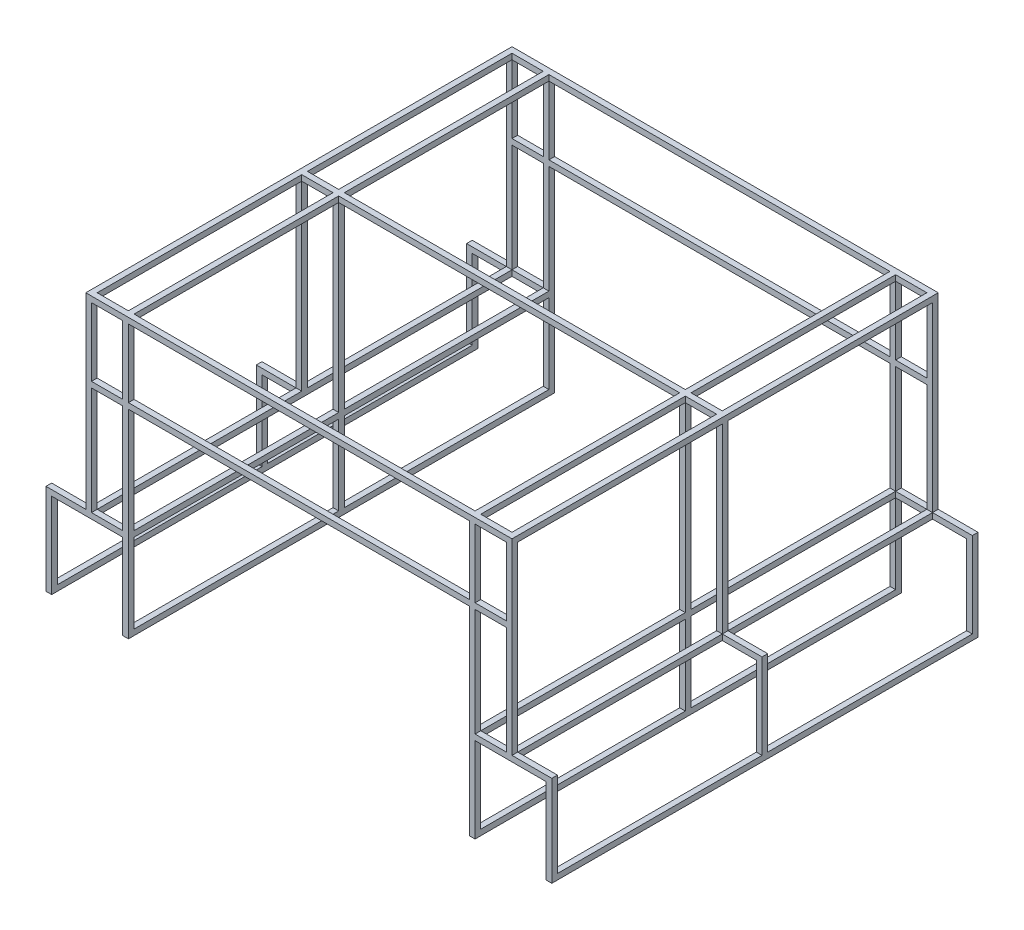
SolidWorks part; units mm, degrees
ref_plane "Front Plane" through (0, 0, 0) normal (0, 0, 1) x (1, 0, 0)
ref_plane "Top Plane" through (0, 0, 0) normal (0, 1, 0) x (1, 0, 0)
ref_plane "Right Plane" through (0, 0, 0) normal (1, 0, 0) x (0, 0, -1)
sketch "Sketch1" plane through (0, 0, 0) normal (0, 1, 0) x (1, 0, 0)
  line L0 (730, 730) -> (730, -730)
  line L1 (750, 750) -> (600, 750)
  line L2 (750, 750) -> (750, -750)
  line L3 (750, -750) -> (600, -750)
  line L4 (600, 750) -> (600, -750)
  line L5 (730, -730) -> (620, -730)
  line L6 (620, 730) -> (620, -730)
  line L7 (730, 730) -> (620, 730)
  point P4 (750, 0)
  dimension "D1" = 600
  dimension "D2" = 150
  dimension "D3" = 1500
  dimension "D4" = 20
extrude "Boss-Extrude1" add sketch "Sketch1" along normal blind 20
sketch "Sketch2" plane through (0, 20, 0) normal (0, 1, 0) x (1, 0, 0)
  line L1 (620, 730) -> (600, 730)
  line L2 (620, 730) -> (620, 750)
  line L3 (620, 750) -> (600, 750)
  line L4 (600, 730) -> (600, 750)
  line L5 (730, 730) -> (750, 730)
  line L6 (730, 730) -> (730, 750)
  line L7 (730, 750) -> (750, 750)
  line L8 (750, 730) -> (750, 750)
  line L9 (600, -750) -> (620, -750)
  line L10 (600, -750) -> (600, -730)
  line L11 (600, -730) -> (620, -730)
  line L12 (620, -750) -> (620, -730)
  line L13 (730, -730) -> (750, -730)
  line L14 (730, -730) -> (730, -750)
  line L15 (730, -750) -> (750, -750)
  line L16 (750, -730) -> (750, -750)
extrude "Boss-Extrude2" add sketch "Sketch2" along normal blind 640
sketch "Sketch3" plane through (0, 660, 0) normal (0, 1, 0) x (1, 0, 0)
  line L0 (620, 730) -> (620, -730)
  line L1 (600, 750) -> (750, 750)
  line L2 (600, 750) -> (600, -750)
  line L3 (600, -750) -> (750, -750)
  line L4 (750, 750) -> (750, -750)
  line L5 (620, -730) -> (730, -730)
  line L6 (730, 730) -> (730, -730)
  line L7 (620, 730) -> (730, 730)
  dimension "D1" = 20
extrude "Boss-Extrude3" add sketch "Sketch3" along normal blind 20
sketch "Sketch4" plane through (0, 0, 0) normal (0, -1, 0) x (1, 0, 0)
  line L0 (730, 730) -> (730, -730) construction
  line L1 (730, 10) -> (750, 10)
  line L2 (730, 10) -> (730, -10)
  line L3 (730, -10) -> (750, -10)
  line L4 (750, 10) -> (750, -10)
  line L5 (750, 750) -> (750, -750) construction
  line L6 (750, -750) -> (600, -750) construction
  line L7 (600, -750) -> (600, 750) construction
  line L8 (600, -10) -> (620, -10)
  line L9 (600, -10) -> (600, 10)
  line L10 (600, 10) -> (620, 10)
  line L11 (620, -10) -> (620, 10)
  line L12 (620, -730) -> (620, 730) construction
  dimension "D1" = 20
  dimension "D2" = 740
extrude "Boss-Extrude4" add sketch "Sketch4" against normal up to surface (660 mm away) up to face at (610, 660, 0)
sketch "Sketch5" plane through (600, 0, 0) normal (-1, 0, 0) x (0, 0, 1)
  line L0 (-750, 680) -> (-750, 0) construction
  line L1 (-750, 420) -> (-730, 420)
  line L2 (-750, 420) -> (-750, 400)
  line L3 (-750, 400) -> (-730, 400)
  line L4 (-730, 420) -> (-730, 400)
  line L5 (-730, 660) -> (-730, 20) construction
  line L6 (-750, 0) -> (750, 0) construction
  line L7 (0, -374) -> (0, 374) construction
  line L8 (-730, 660) -> (-750, 660)
  line L9 (-730, 660) -> (-730, 680)
  line L10 (-730, 680) -> (-750, 680)
  line L11 (-750, 660) -> (-750, 680)
  line L12 (750, 420) -> (750, 400)
  line L13 (750, 400) -> (730, 400)
  line L14 (730, 420) -> (730, 400)
  line L15 (750, 420) -> (730, 420)
  line L16 (730, 680) -> (750, 680)
  line L17 (750, 660) -> (750, 680)
  line L18 (730, 660) -> (750, 660)
  line L19 (730, 660) -> (730, 680)
  line L20 (-750, 680) -> (750, 680) construction
  line L21 (-10, 660) -> (10, 660)
  line L22 (-10, 660) -> (-10, 680)
  line L23 (-10, 680) -> (10, 680)
  line L24 (10, 660) -> (10, 680)
  line L25 (10, 660) -> (10, 20) construction
  dimension "D1" = 20
  dimension "D2" = 400
extrude "Boss-Extrude5" add sketch "Sketch5" along normal blind 600 and the other way up to surface (130 mm away) other way up to face at (730, 340, -740)
sketch "Sketch6" plane through (0, 0, 0) normal (0, -1, 0) x (1, 0, 0)
  line L1 (750, 750) -> (890, 750)
  line L2 (750, 750) -> (750, 730)
  line L3 (750, 730) -> (890, 730)
  line L4 (890, 750) -> (890, 730)
  line L5 (750, 10) -> (890, 10)
  line L6 (750, 10) -> (750, -10)
  line L7 (750, -10) -> (890, -10)
  line L8 (890, 10) -> (890, -10)
  line L9 (750, -750) -> (890, -750)
  line L10 (750, -750) -> (750, -730)
  line L11 (750, -730) -> (890, -730)
  line L12 (890, -750) -> (890, -730)
  point P15 (0, 0)
  dimension "D1" = 20
  dimension "D2" = 20
  dimension "D3" = 20
  dimension "D4" = 140
extrude "Boss-Extrude6" add sketch "Sketch6" against normal blind 20
sketch "Sketch7" plane through (0, 0, 0) normal (0, -1, 0) x (1, 0, 0)
  line L0 (600, 750) -> (890, 750) construction
  line L5 (600, 750) -> (620, 750)
  line L6 (600, 750) -> (600, 730)
  line L7 (600, 730) -> (620, 730)
  line L8 (620, 750) -> (620, 730)
  line L9 (890, 730) -> (870, 730)
  line L10 (890, 730) -> (890, 750)
  line L11 (890, 750) -> (870, 750)
  line L12 (870, 730) -> (870, 750)
  line L13 (890, -730) -> (750, -730) construction
  line L14 (600, 10) -> (620, 10)
  line L15 (600, 10) -> (600, -10)
  line L16 (600, -10) -> (620, -10)
  line L17 (620, 10) -> (620, -10)
  line L18 (600, -750) -> (620, -750)
  line L19 (600, -750) -> (600, -730)
  line L20 (600, -730) -> (620, -730)
  line L21 (620, -750) -> (620, -730)
  line L22 (890, -750) -> (870, -750)
  line L23 (890, -750) -> (890, -730)
  line L24 (890, -730) -> (870, -730)
  line L25 (870, -750) -> (870, -730)
  line L26 (890, 10) -> (750, 10) construction
  line L27 (890, -10) -> (870, -10)
  line L28 (890, -10) -> (890, 10)
  line L29 (890, 10) -> (870, 10)
  line L30 (870, -10) -> (870, 10)
  dimension "D1" = 20
  dimension "D2" = 20
  dimension "D3" = 20
extrude "Boss-Extrude7" add sketch "Sketch7" along normal blind 300
sketch "Sketch8" plane through (0, 0, 750) normal (0, 0, 1) x (1, 0, 0)
  line L0 (620, -300) -> (620, 0) construction
  line L1 (600, -300) -> (620, -300)
  line L2 (600, -300) -> (600, -280)
  line L3 (600, -280) -> (620, -280)
  line L4 (620, -300) -> (620, -280)
  line L5 (890, 20) -> (890, -300) construction
  line L6 (870, -300) -> (890, -300)
  line L7 (870, -300) -> (870, -280)
  line L8 (870, -280) -> (890, -280)
  line L9 (890, -300) -> (890, -280)
  dimension "D1" = 20
  dimension "D2" = 20
extrude "Boss-Extrude8" add sketch "Sketch8" against normal through all
mirror "Mirror1" about plane through (0, 0, 0) normal (1, 0, 0) of bodies 109 105
